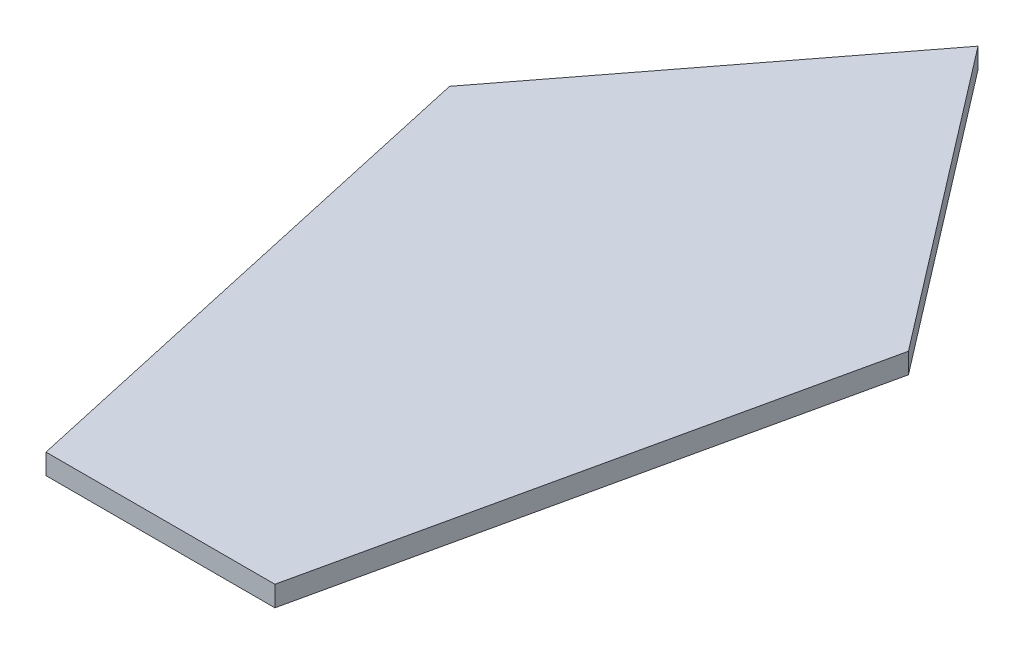
SolidWorks part; units mm, degrees
ref_plane "Front Plane" through (0, 0, 0) normal (0, 0, 1) x (1, 0, 0)
ref_plane "Top Plane" through (0, 0, 0) normal (0, 1, 0) x (1, 0, 0)
ref_plane "Right Plane" through (0, 0, 0) normal (1, 0, 0) x (0, 0, -1)
sketch "Sketch1" plane through (0, 0, 0) normal (0, 1, 0) x (1, 0, 0)
  line L0 (-17.78, 0) -> (17.78, 0)
  line L1 (17.78, 0) -> (35.6386, 80.5549)
  line L2 (35.6386, 80.5549) -> (0, 127)
  line L3 (0, 127) -> (-35.6386, 80.5549)
  line L4 (-35.6386, 80.5549) -> (-17.78, 0)
  point P6 (0, 0)
  dimension "D1" = 75
  dimension "D2" = 130
  dimension "D3" = 130
  dimension "D4" = 127
  dimension "D5" = 35.56
  dimension "D6" = 17.8586
extrude "Boss-Extrude1" add sketch "Sketch1" along normal blind 3.175
equation "\"D3@Sketch1\"=\"D2@Sketch1\""
